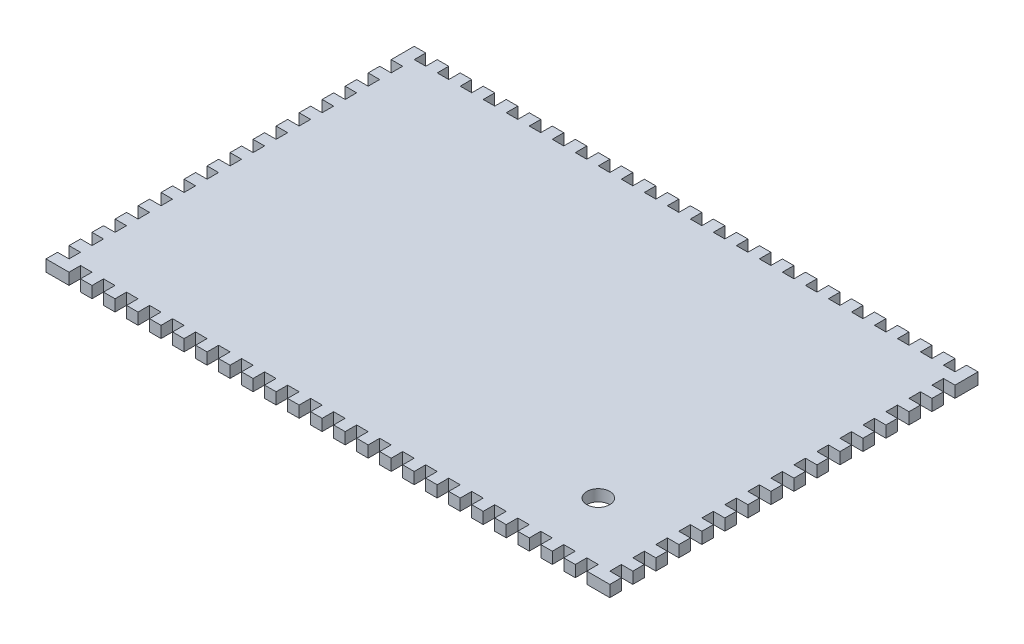
SolidWorks part; units mm, degrees
ref_plane "Alzado" through (0, 0, 0) normal (0, 0, 1) x (1, 0, 0)
ref_plane "Planta" through (0, 0, 0) normal (0, 1, 0) x (1, 0, 0)
ref_plane "Vista lateral" through (0, 0, 0) normal (1, 0, 0) x (0, 0, -1)
sketch "Croquis1" plane through (0, 0, 0) normal (0, 1, 0) x (1, 0, 0)
  line L0 (5, 110) -> (0, 110)
  line L1 (0, 0) -> (5, 0)
  line L2 (5, 20) -> (0, 20)
  line L3 (5, 15) -> (5, 20)
  line L4 (5, 105) -> (5, 110)
  line L5 (235, 0) -> (245, 0)
  line L6 (0, 0) -> (0, 5)
  line L7 (0, 5) -> (5, 5)
  line L8 (5, 5) -> (5, 10)
  line L9 (5, 10) -> (0, 10)
  line L10 (0, 15) -> (5, 15)
  line L11 (0, 10) -> (0, 15)
  line L12 (5, 30) -> (0, 30)
  line L13 (5, 25) -> (5, 30)
  line L14 (0, 25) -> (5, 25)
  line L15 (0, 20) -> (0, 25)
  line L16 (5, 40) -> (0, 40)
  line L17 (5, 35) -> (5, 40)
  line L18 (0, 35) -> (5, 35)
  line L19 (0, 30) -> (0, 35)
  line L20 (5, 50) -> (0, 50)
  line L21 (5, 45) -> (5, 50)
  line L22 (0, 45) -> (5, 45)
  line L23 (0, 40) -> (0, 45)
  line L24 (5, 60) -> (0, 60)
  line L25 (5, 55) -> (5, 60)
  line L26 (0, 55) -> (5, 55)
  line L27 (0, 50) -> (0, 55)
  line L28 (5, 70) -> (0, 70)
  line L29 (5, 65) -> (5, 70)
  line L30 (0, 65) -> (5, 65)
  line L31 (0, 60) -> (0, 65)
  line L32 (5, 80) -> (0, 80)
  line L33 (5, 75) -> (5, 80)
  line L34 (0, 75) -> (5, 75)
  line L35 (0, 70) -> (0, 75)
  line L36 (5, 90) -> (0, 90)
  line L37 (5, 85) -> (5, 90)
  line L38 (0, 85) -> (5, 85)
  line L39 (0, 80) -> (0, 85)
  line L40 (5, 100) -> (0, 100)
  line L41 (5, 95) -> (5, 100)
  line L42 (0, 95) -> (5, 95)
  line L43 (0, 90) -> (0, 95)
  line L44 (0, 105) -> (5, 105)
  line L45 (0, 100) -> (0, 105)
  line L46 (5, 120) -> (0, 120)
  line L47 (5, 115) -> (5, 120)
  line L48 (0, 115) -> (5, 115)
  line L49 (0, 110) -> (0, 115)
  line L50 (5, 130) -> (0, 130)
  line L51 (5, 125) -> (5, 130)
  line L52 (0, 125) -> (5, 125)
  line L53 (0, 120) -> (0, 125)
  line L54 (5, 140) -> (0, 140)
  line L55 (5, 135) -> (5, 140)
  line L56 (0, 135) -> (5, 135)
  line L57 (0, 130) -> (0, 135)
  line L58 (5, 150) -> (0, 150)
  line L59 (5, 145) -> (5, 150)
  line L60 (0, 145) -> (5, 145)
  line L61 (0, 140) -> (0, 145)
  line L62 (5, 0) -> (10, 0)
  line L63 (10, 0) -> (10, 5)
  line L64 (10, 5) -> (15, 5)
  line L65 (15, 5) -> (15, 0)
  line L66 (15, 0) -> (20, 0)
  line L67 (20, 0) -> (20, 5)
  line L68 (25, 5) -> (25, 0)
  line L69 (20, 5) -> (25, 5)
  line L70 (25, 0) -> (30, 0)
  line L71 (30, 0) -> (30, 5)
  line L72 (35, 5) -> (35, 0)
  line L73 (30, 5) -> (35, 5)
  line L74 (35, 0) -> (40, 0)
  line L75 (40, 0) -> (40, 5)
  line L76 (45, 5) -> (45, 0)
  line L77 (40, 5) -> (45, 5)
  line L78 (45, 0) -> (50, 0)
  line L79 (50, 0) -> (50, 5)
  line L80 (55, 5) -> (55, 0)
  line L81 (50, 5) -> (55, 5)
  line L82 (55, 0) -> (60, 0)
  line L83 (60, 0) -> (60, 5)
  line L84 (65, 5) -> (65, 0)
  line L85 (235, 155) -> (240, 155)
  line L86 (60, 5) -> (65, 5)
  line L87 (65, 0) -> (70, 0)
  line L88 (70, 0) -> (70, 5)
  line L89 (75, 5) -> (75, 0)
  line L90 (70, 5) -> (75, 5)
  line L91 (75, 0) -> (80, 0)
  line L92 (80, 0) -> (80, 5)
  line L93 (85, 5) -> (85, 0)
  line L94 (80, 5) -> (85, 5)
  line L95 (85, 0) -> (90, 0)
  line L96 (90, 0) -> (90, 5)
  line L97 (95, 5) -> (95, 0)
  line L98 (90, 5) -> (95, 5)
  line L99 (95, 0) -> (100, 0)
  line L100 (100, 0) -> (100, 5)
  line L101 (105, 5) -> (105, 0)
  line L102 (100, 5) -> (105, 5)
  line L103 (105, 0) -> (110, 0)
  line L104 (110, 0) -> (110, 5)
  line L105 (115, 5) -> (115, 0)
  line L106 (110, 5) -> (115, 5)
  line L107 (115, 0) -> (120, 0)
  line L108 (120, 0) -> (120, 5)
  line L109 (125, 5) -> (125, 0)
  line L110 (120, 5) -> (125, 5)
  line L111 (125, 0) -> (130, 0)
  line L112 (130, 0) -> (130, 5)
  line L113 (135, 5) -> (135, 0)
  line L114 (130, 5) -> (135, 5)
  line L115 (135, 0) -> (140, 0)
  line L116 (140, 0) -> (140, 5)
  line L117 (145, 5) -> (145, 0)
  line L118 (140, 5) -> (145, 5)
  line L119 (145, 0) -> (150, 0)
  line L120 (150, 0) -> (150, 5)
  line L121 (155, 5) -> (155, 0)
  line L122 (150, 5) -> (155, 5)
  line L123 (155, 0) -> (160, 0)
  line L124 (160, 0) -> (160, 5)
  line L125 (165, 5) -> (165, 0)
  line L126 (160, 5) -> (165, 5)
  line L127 (165, 0) -> (170, 0)
  line L128 (170, 0) -> (170, 5)
  line L129 (175, 5) -> (175, 0)
  line L130 (170, 5) -> (175, 5)
  line L131 (175, 0) -> (180, 0)
  line L132 (180, 0) -> (180, 5)
  line L133 (185, 5) -> (185, 0)
  line L134 (180, 5) -> (185, 5)
  line L135 (185, 0) -> (190, 0)
  line L136 (190, 0) -> (190, 5)
  line L137 (195, 5) -> (195, 0)
  line L138 (190, 5) -> (195, 5)
  line L139 (195, 0) -> (200, 0)
  line L140 (200, 0) -> (200, 5)
  line L141 (205, 5) -> (205, 0)
  line L142 (200, 5) -> (205, 5)
  line L143 (205, 0) -> (210, 0)
  line L144 (210, 0) -> (210, 5)
  line L145 (215, 5) -> (215, 0)
  line L146 (210, 5) -> (215, 5)
  line L147 (215, 0) -> (220, 0)
  line L148 (220, 0) -> (220, 5)
  line L149 (225, 5) -> (225, 0)
  line L150 (220, 5) -> (225, 5)
  line L151 (225, 0) -> (230, 0)
  line L152 (230, 0) -> (230, 5)
  line L153 (235, 5) -> (235, 0)
  line L154 (230, 5) -> (235, 5)
  line L155 (240, 155) -> (240, 160)
  line L156 (240, 160) -> (245, 160)
  line L157 (245, 160) -> (245, 150)
  line L158 (0, 150) -> (0, 160)
  line L159 (0, 160) -> (5, 160)
  line L160 (5, 155) -> (10, 155)
  line L161 (10, 155) -> (10, 160)
  line L162 (10, 160) -> (15, 160)
  line L163 (245, 140) -> (245, 145)
  line L164 (245, 145) -> (240, 145)
  line L165 (240, 145) -> (240, 150)
  line L166 (240, 150) -> (245, 150)
  line L167 (245, 130) -> (245, 135)
  line L168 (245, 135) -> (240, 135)
  line L169 (240, 135) -> (240, 140)
  line L170 (240, 140) -> (245, 140)
  line L171 (245, 120) -> (245, 125)
  line L172 (245, 125) -> (240, 125)
  line L173 (240, 125) -> (240, 130)
  line L174 (240, 130) -> (245, 130)
  line L175 (245, 110) -> (245, 115)
  line L176 (245, 115) -> (240, 115)
  line L177 (240, 115) -> (240, 120)
  line L178 (240, 120) -> (245, 120)
  line L179 (245, 100) -> (245, 105)
  line L180 (245, 105) -> (240, 105)
  line L181 (245, 90) -> (245, 95)
  line L182 (245, 95) -> (240, 95)
  line L183 (240, 95) -> (240, 100)
  line L184 (240, 100) -> (245, 100)
  line L185 (245, 80) -> (245, 85)
  line L186 (245, 85) -> (240, 85)
  line L187 (240, 85) -> (240, 90)
  line L188 (240, 90) -> (245, 90)
  line L189 (245, 70) -> (245, 75)
  line L190 (245, 75) -> (240, 75)
  line L191 (240, 75) -> (240, 80)
  line L192 (240, 80) -> (245, 80)
  line L193 (245, 60) -> (245, 65)
  line L194 (245, 65) -> (240, 65)
  line L195 (240, 65) -> (240, 70)
  line L196 (240, 70) -> (245, 70)
  line L197 (245, 50) -> (245, 55)
  line L198 (245, 55) -> (240, 55)
  line L199 (240, 55) -> (240, 60)
  line L200 (240, 60) -> (245, 60)
  line L201 (245, 40) -> (245, 45)
  line L202 (245, 45) -> (240, 45)
  line L203 (240, 45) -> (240, 50)
  line L204 (240, 50) -> (245, 50)
  line L205 (245, 30) -> (245, 35)
  line L206 (245, 35) -> (240, 35)
  line L207 (240, 35) -> (240, 40)
  line L208 (240, 40) -> (245, 40)
  line L209 (245, 20) -> (245, 25)
  line L210 (245, 25) -> (240, 25)
  line L211 (240, 25) -> (240, 30)
  line L212 (240, 30) -> (245, 30)
  line L213 (245, 10) -> (245, 15)
  line L214 (245, 15) -> (240, 15)
  line L215 (240, 10) -> (245, 10)
  line L216 (240, 5) -> (240, 10)
  line L217 (245, 5) -> (240, 5)
  line L218 (245, 0) -> (245, 5)
  line L219 (240, 105) -> (240, 110)
  line L220 (240, 15) -> (240, 20)
  line L221 (240, 20) -> (245, 20)
  line L222 (240, 110) -> (245, 110)
  line L223 (15, 160) -> (15, 155)
  line L224 (15, 155) -> (20, 155)
  line L225 (20, 155) -> (20, 160)
  line L226 (25, 160) -> (25, 155)
  line L227 (20, 160) -> (25, 160)
  line L228 (25, 155) -> (30, 155)
  line L229 (30, 155) -> (30, 160)
  line L230 (35, 160) -> (35, 155)
  line L231 (30, 160) -> (35, 160)
  line L232 (35, 155) -> (40, 155)
  line L233 (40, 155) -> (40, 160)
  line L234 (45, 160) -> (45, 155)
  line L235 (40, 160) -> (45, 160)
  line L236 (45, 155) -> (50, 155)
  line L237 (50, 155) -> (50, 160)
  line L238 (55, 160) -> (55, 155)
  line L239 (50, 160) -> (55, 160)
  line L240 (55, 155) -> (60, 155)
  line L241 (60, 155) -> (60, 160)
  line L242 (65, 160) -> (65, 155)
  line L243 (60, 160) -> (65, 160)
  line L244 (65, 155) -> (70, 155)
  line L245 (70, 155) -> (70, 160)
  line L246 (75, 160) -> (75, 155)
  line L247 (70, 160) -> (75, 160)
  line L248 (75, 155) -> (80, 155)
  line L249 (80, 155) -> (80, 160)
  line L250 (85, 160) -> (85, 155)
  line L251 (80, 160) -> (85, 160)
  line L252 (85, 155) -> (90, 155)
  line L253 (90, 155) -> (90, 160)
  line L254 (95, 160) -> (95, 155)
  line L255 (90, 160) -> (95, 160)
  line L256 (95, 155) -> (100, 155)
  line L257 (100, 155) -> (100, 160)
  line L258 (105, 160) -> (105, 155)
  line L259 (100, 160) -> (105, 160)
  line L260 (105, 155) -> (110, 155)
  line L261 (110, 155) -> (110, 160)
  line L262 (115, 160) -> (115, 155)
  line L263 (110, 160) -> (115, 160)
  line L264 (115, 155) -> (120, 155)
  line L265 (120, 155) -> (120, 160)
  line L266 (125, 160) -> (125, 155)
  line L267 (120, 160) -> (125, 160)
  line L268 (125, 155) -> (130, 155)
  line L269 (130, 155) -> (130, 160)
  line L270 (135, 160) -> (135, 155)
  line L271 (130, 160) -> (135, 160)
  line L272 (135, 155) -> (140, 155)
  line L273 (140, 155) -> (140, 160)
  line L274 (145, 160) -> (145, 155)
  line L275 (140, 160) -> (145, 160)
  line L276 (145, 155) -> (150, 155)
  line L277 (150, 155) -> (150, 160)
  line L278 (155, 160) -> (155, 155)
  line L279 (150, 160) -> (155, 160)
  line L280 (155, 155) -> (160, 155)
  line L281 (160, 155) -> (160, 160)
  line L282 (165, 160) -> (165, 155)
  line L283 (160, 160) -> (165, 160)
  line L284 (165, 155) -> (170, 155)
  line L285 (170, 155) -> (170, 160)
  line L286 (175, 160) -> (175, 155)
  line L287 (170, 160) -> (175, 160)
  line L288 (175, 155) -> (180, 155)
  line L289 (180, 155) -> (180, 160)
  line L290 (185, 160) -> (185, 155)
  line L291 (180, 160) -> (185, 160)
  line L292 (185, 155) -> (190, 155)
  line L293 (190, 155) -> (190, 160)
  line L294 (195, 160) -> (195, 155)
  line L295 (190, 160) -> (195, 160)
  line L296 (195, 155) -> (200, 155)
  line L297 (200, 155) -> (200, 160)
  line L298 (205, 160) -> (205, 155)
  line L299 (200, 160) -> (205, 160)
  line L300 (205, 155) -> (210, 155)
  line L301 (210, 155) -> (210, 160)
  line L302 (215, 160) -> (215, 155)
  line L303 (210, 160) -> (215, 160)
  line L304 (215, 155) -> (220, 155)
  line L305 (220, 155) -> (220, 160)
  line L306 (225, 160) -> (225, 155)
  line L307 (220, 160) -> (225, 160)
  line L308 (225, 155) -> (230, 155)
  line L309 (230, 155) -> (230, 160)
  line L310 (235, 160) -> (235, 155)
  line L311 (230, 160) -> (235, 160)
  line L312 (5, 160) -> (5, 155)
  line L316 (5, 165) -> (0, 165) [skipped]
  line L317 (5, 160) -> (5, 165) [skipped]
  line L318 (0, 155) -> (0, 160) [skipped]
  line L319 (0, 160) -> (5, 160) [skipped]
  line L320 (0, 155) -> (5, 155) [skipped]
  line L321 (235, 155) -> (245, 155) [skipped]
  line L322 (245, 160) -> (240, 160) [skipped]
  line L323 (240, 160) -> (240, 165) [skipped]
  line L324 (240, 165) -> (245, 165) [skipped]
  line L325 (245, 155) -> (245, 160) [skipped]
  circle A0 centre (210, 30) radius 5
  dimension "D17" = 10
  dimension "D1" = 5
  dimension "D2" = 245
  dimension "D3" = 5
  dimension "D4" = 5
  dimension "D5" = 5
  dimension "D7" = 5
  dimension "D8" = 5
  dimension "D9" = 5
  dimension "D10" = 5
  dimension "D11" = 5
  dimension "D12" = 23
  dimension "D13" = 5
  dimension "D14" = 5
  dimension "D15" = 2
  dimension "D16" = 160
  dimension "D6" = 15
extrude "Saliente-Extruir1" add sketch "Croquis1" along normal blind 5
